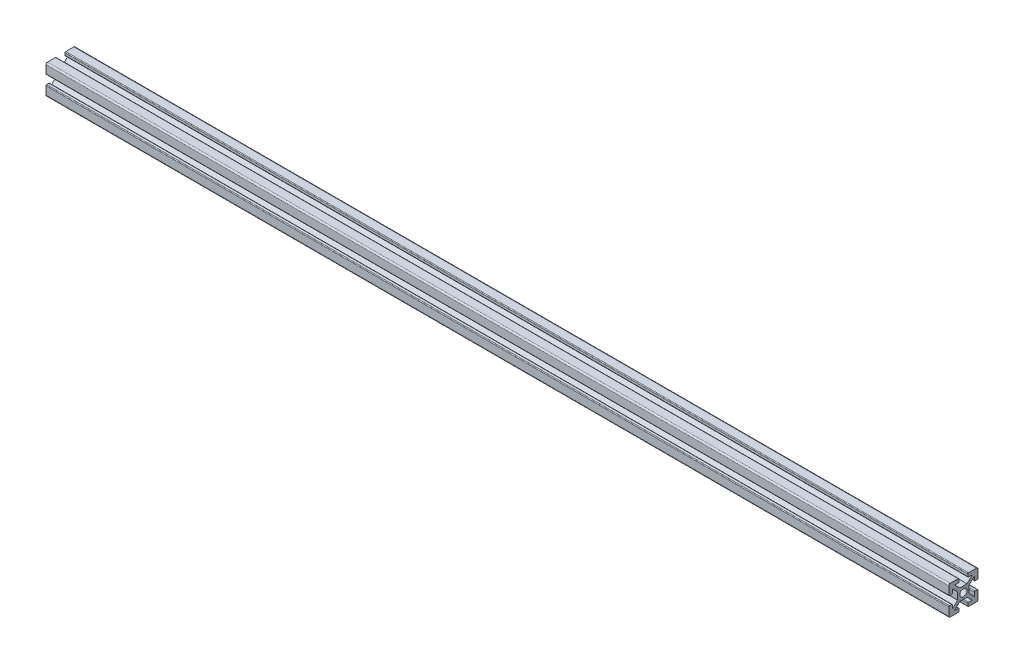
SolidWorks part; units mm, degrees
ref_plane "Front Plane" through (0, 0, 0) normal (0, 0, 1) x (1, 0, 0)
ref_plane "Top Plane" through (0, 0, 0) normal (0, 1, 0) x (1, 0, 0)
ref_plane "Right Plane" through (0, 0, 0) normal (1, 0, 0) x (0, 0, -1)
sketch "Sketch1" plane through (0, 0, 0) normal (0, 0, 1) x (1, 0, 0)
  line L0 (-286.3505, 0) -> (333.6495, 0)
  dimension "D1" = 620
other "Aluminium prof ALUMINIUM PROF(1)"
ref_plane "Plane1" through (-286.3505, 0, 0) normal (1, 0, 0) x (0, 1, 0)
sketch "Sketch11" plane through (-286.3505, 0, 0) normal (1, 0, 0) x (0, 1, 0)
  line L0 (0, 0) -> (0, 19.0058) construction
  line L9 (0, 0) -> (23.0409, 0) construction
  line L10 (23.0409, 0) -> (23.0409, -0.0585) construction
  line L11 (23.0409, -0.0585) -> (23.0409, 0) construction
  line L13 (-2.5, 4) -> (2.5, 4)
  line L14 (2.5, 4) -> (6.0355, 7.5355)
  line L15 (6.0355, 7.5355) -> (3.5355, 7.5355)
  line L16 (3.0355, 8.0355) -> (3.0355, 9.5355)
  line L17 (3.5355, 10.0355) -> (9.0355, 10.0355)
  line L18 (10.0355, 9.0355) -> (10.0355, 3.5355)
  line L19 (9.5355, 3.0355) -> (8.0355, 3.0355)
  line L20 (7.5355, 3.5355) -> (7.5355, 6.0355)
  line L21 (7.5355, 6.0355) -> (4, 2.5)
  line L22 (4, 2.5) -> (4, -2.5)
  line L23 (-10.0355, 9.0355) -> (-10.0355, 3.5355)
  line L24 (-4, 2.5) -> (-4, -2.5)
  line L25 (-7.5355, 6.0355) -> (-4, 2.5)
  line L26 (-7.5355, 3.5355) -> (-7.5355, 6.0355)
  line L27 (-9.5355, 3.0355) -> (-8.0355, 3.0355)
  line L28 (-3.5355, 10.0355) -> (-9.0355, 10.0355)
  line L29 (-3.0355, 8.0355) -> (-3.0355, 9.5355)
  line L30 (-6.0355, 7.5355) -> (-3.5355, 7.5355)
  line L31 (-2.5, 4) -> (-6.0355, 7.5355)
  line L32 (3.5355, -10.0355) -> (9.0355, -10.0355)
  line L33 (-2.5, -4) -> (-6.0355, -7.5355)
  line L34 (-6.0355, -7.5355) -> (-3.5355, -7.5355)
  line L35 (-3.0355, -8.0355) -> (-3.0355, -9.5355)
  line L36 (-3.5355, -10.0355) -> (-9.0355, -10.0355)
  line L37 (-9.5355, -3.0355) -> (-8.0355, -3.0355)
  line L38 (-7.5355, -3.5355) -> (-7.5355, -6.0355)
  line L39 (-7.5355, -6.0355) -> (-4, -2.5)
  line L40 (-10.0355, -9.0355) -> (-10.0355, -3.5355)
  line L41 (7.5355, -6.0355) -> (4, -2.5)
  line L42 (7.5355, -3.5355) -> (7.5355, -6.0355)
  line L43 (9.5355, -3.0355) -> (8.0355, -3.0355)
  line L44 (10.0355, -9.0355) -> (10.0355, -3.5355)
  line L45 (3.0355, -8.0355) -> (3.0355, -9.5355)
  line L46 (6.0355, -7.5355) -> (3.5355, -7.5355)
  line L47 (2.5, -4) -> (6.0355, -7.5355)
  line L48 (-2.5, -4) -> (2.5, -4)
  circle A0 centre (0, 0) radius 2.5
  arc A1 (-10.0355, 9.0355) -> (-9.0355, 10.0355) centre (-9.0355, 9.0355) cw
  arc A2 (-9.0355, -10.0355) -> (-10.0355, -9.0355) centre (-9.0355, -9.0355) cw
  arc A3 (9.0355, -10.0355) -> (10.0355, -9.0355) centre (9.0355, -9.0355) ccw
  arc A4 (9.0355, 10.0355) -> (10.0355, 9.0355) centre (9.0355, 9.0355) cw
  arc A5 (-9.5355, -3.0355) -> (-10.0355, -3.5355) centre (-9.5355, -3.5355) ccw
  arc A6 (-8.0355, -3.0355) -> (-7.5355, -3.5355) centre (-8.0355, -3.5355) cw
  arc A7 (-3.5355, -7.5355) -> (-3.0355, -8.0355) centre (-3.5355, -8.0355) cw
  arc A8 (-3.0355, -9.5355) -> (-3.5355, -10.0355) centre (-3.5355, -9.5355) cw
  arc A9 (3.5355, -10.0355) -> (3.0355, -9.5355) centre (3.5355, -9.5355) cw
  arc A10 (3.0355, -8.0355) -> (3.5355, -7.5355) centre (3.5355, -8.0355) cw
  arc A11 (9.5355, -3.0355) -> (10.0355, -3.5355) centre (9.5355, -3.5355) cw
  arc A12 (7.5355, -3.5355) -> (8.0355, -3.0355) centre (8.0355, -3.5355) cw
  arc A13 (10.0355, 3.5355) -> (9.5355, 3.0355) centre (9.5355, 3.5355) cw
  arc A14 (8.0355, 3.0355) -> (7.5355, 3.5355) centre (8.0355, 3.5355) cw
  arc A15 (3.5355, 7.5355) -> (3.0355, 8.0355) centre (3.5355, 8.0355) cw
  arc A16 (3.0355, 9.5355) -> (3.5355, 10.0355) centre (3.5355, 9.5355) cw
  arc A17 (-3.5355, 10.0355) -> (-3.0355, 9.5355) centre (-3.5355, 9.5355) cw
  arc A18 (-3.0355, 8.0355) -> (-3.5355, 7.5355) centre (-3.5355, 8.0355) cw
  arc A19 (-7.5355, 3.5355) -> (-8.0355, 3.0355) centre (-8.0355, 3.5355) cw
  arc A20 (-10.0355, 3.5355) -> (-9.5355, 3.0355) centre (-9.5355, 3.5355) ccw
  point P26 (0, 4)
  point P29 (-4, 0)
  point P30 (4, 0)
  point P44 (0, -4)
  point P48 (-10.0355, 10.0355)
  point P51 (-10.0355, -10.0355)
  point P54 (10.0355, -10.0355)
  point P57 (10.0355, 10.0355)
  point P60 (-10.0355, -3.0355)
  point P63 (-7.5355, -3.0355)
  point P66 (-3.0355, -7.5355)
  point P69 (-3.0355, -10.0355)
  point P72 (3.0355, -10.0355)
  point P75 (3.0355, -7.5355)
  point P78 (10.0355, -3.0355)
  point P81 (7.5355, -3.0355)
  point P84 (10.0355, 3.0355)
  point P87 (7.5355, 3.0355)
  point P90 (3.0355, 7.5355)
  point P93 (3.0355, 10.0355)
  point P96 (-3.0355, 10.0355)
  point P99 (-3.0355, 7.5355)
  point P102 (-7.5355, 3.0355)
  point P105 (-10.0355, 3.0355)
  point P106 (0, 0)
  dimension "D5" = 4
  dimension "D12" = 1
  dimension "D13" = 0.5
  dimension "D1" = 135
  dimension "D2" = 2.5
  dimension "D3" = 4
  dimension "D4" = 2.5
  dimension "D6" = 7
  dimension "D7" = 7
  dimension "D8" = 3
  dimension "D9" = 3
  dimension "D10" = 5
  dimension "D11" = 23.0409
